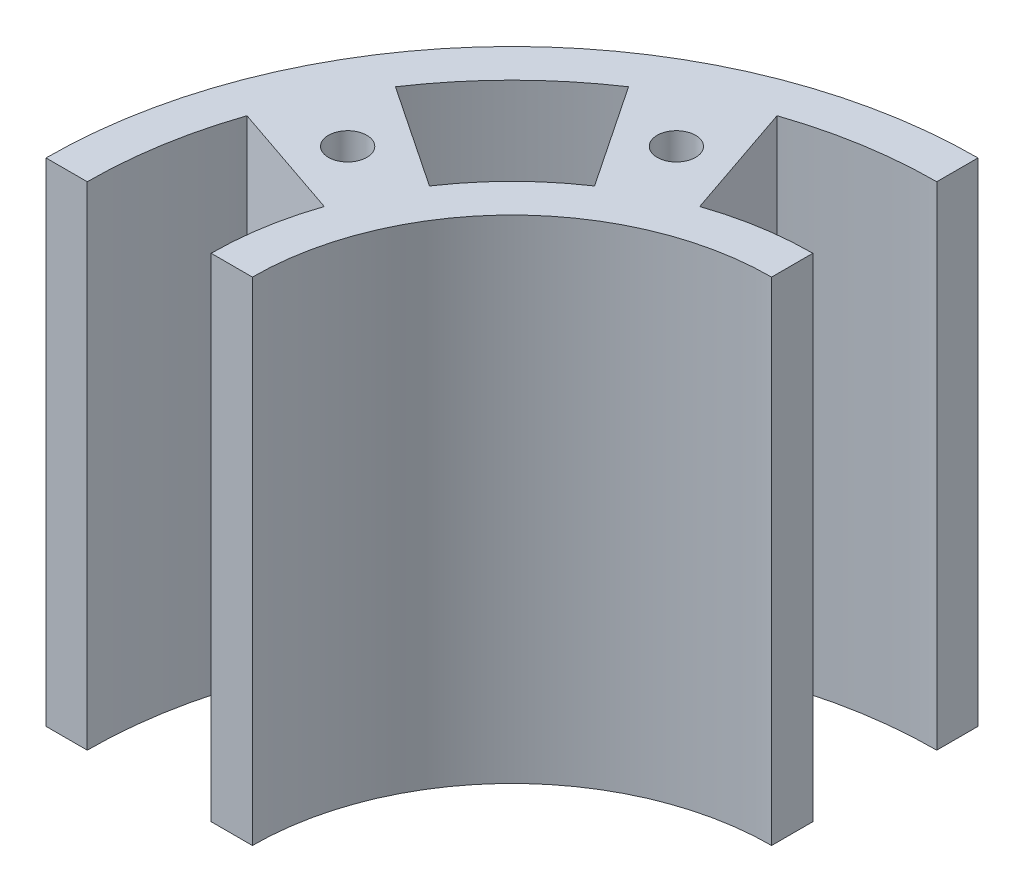
SolidWorks part; units mm, degrees
ref_plane "Front Plane" through (0, 0, 0) normal (0, 0, 1) x (1, 0, 0)
ref_plane "Top Plane" through (0, 0, 0) normal (0, 1, 0) x (1, 0, 0)
ref_plane "Right Plane" through (0, 0, 0) normal (1, 0, 0) x (0, 0, -1)
sketch "Sketch2" plane through (0, 0, 0) normal (0, 1, 0) x (1, 0, 0)
  line L0 (60, -60) -> (35.32, -60)
  line L1 (0, 0) -> (60, 0)
  line L2 (0, 0) -> (0, -60)
  line L3 (0, -60) -> (60, -60)
  line L4 (60, 0) -> (60, -60)
  line L5 (35.32, -60) -> (60, -35.32)
  line L6 (60, -60) -> (0, 0) construction
  line L7 (60, -60) -> (37.5294, -26.4498)
  line L8 (60, -60) -> (26.4498, -37.5294)
  line L9 (60, -60) -> (18.0681, -45.7099)
  line L10 (18.0681, -45.7099) -> (60, -60)
  line L11 (60, -60) -> (45.7099, -18.0681)
  circle A0 centre (60, -60) radius 24.68
  circle A1 centre (44.71, -29.0844) radius 1.825
  circle A2 centre (29.0844, -44.71) radius 1.825
  circle A3 centre (60, -60) radius 44.3
  circle A4 centre (60, -60) radius 28.6
  circle A5 centre (60, -60) radius 40.38
  dimension "D7" = 3.65
  dimension "D8" = 88.6
  dimension "D9" = 57.2
  dimension "D10" = 80.76
  dimension "D1" = 24.68
  dimension "D2" = 24.68
  dimension "D3" = 60
  dimension "D4" = 60
  dimension "D5" = 15.29
  dimension "D6" = 34.49
  dimension "D11" = 4.5
  dimension "D12" = 4.5
  dimension "D13" = 4.5
  dimension "D14" = 4.5
extrude "Boss-Extrude2" add sketch "Sketch2" along normal blind 46.8 contours L11 A5 L7 A4 A1 | L8 A5 L9 A4 A2 | L6 A5 L11 A3 | A5 L4 A3 L11 | L4 A4 L11 A0 | L11 A4 L7 A0 | L6 A0 L7 A4 | A0 L6 A4 L8 | A5 L6 A3 L10 | A5 L10 A3 L3 | L10 A4 L3 A0 | L8 A4 L10 A0
